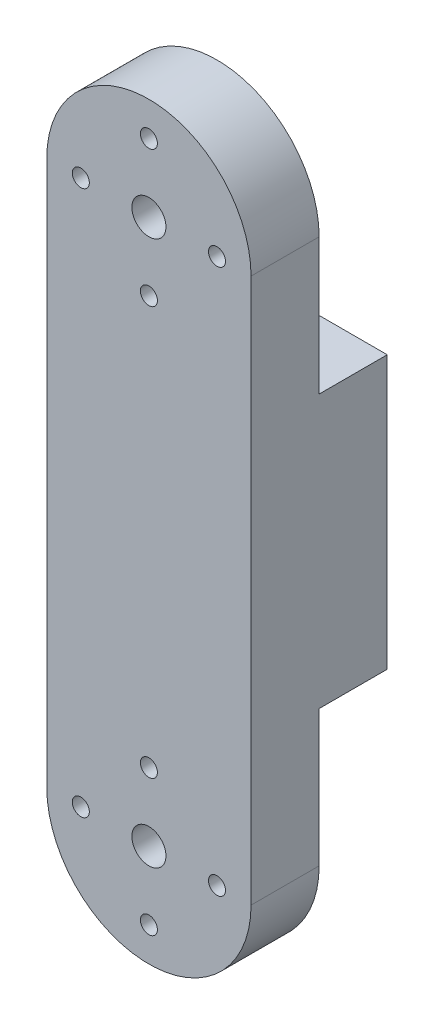
SolidWorks part; units mm, degrees
ref_plane "Front Plane" through (0, 0, 0) normal (0, 0, 1) x (1, 0, 0)
ref_plane "Top Plane" through (0, 0, 0) normal (0, 1, 0) x (1, 0, 0)
ref_plane "Right Plane" through (0, 0, 0) normal (1, 0, 0) x (0, 0, -1)
sketch "Sketch1" plane through (0, 0, 0) normal (0, 0, 1) x (1, 0, 0)
  line L0 (-19.05, 50.8) -> (-19.05, -50.8)
  line L1 (19.05, 50.8) -> (19.05, -50.8)
  line L2 (0, 50.8) -> (0, -50.8) construction
  line L3 (0, 38.1) -> (0, 63.5) construction
  line L4 (-12.7, 50.8) -> (12.7, 50.8) construction
  line L5 (0, -38.1) -> (0, -63.5) construction
  line L6 (-12.7, -50.8) -> (12.7, -50.8) construction
  arc A0 (-19.05, 50.8) -> (19.05, 50.8) centre (0, 50.8) cw
  arc A1 (-19.05, -50.8) -> (19.05, -50.8) centre (0, -50.8) ccw
  circle A2 centre (0, 50.8) radius 3.175
  circle A3 centre (0, -50.8) radius 3.175
  circle A4 centre (0, 63.5) radius 1.5875
  circle A5 centre (-12.7, 50.8) radius 1.5875
  circle A6 centre (0, 38.1) radius 1.5875
  circle A7 centre (12.7, 50.8) radius 1.5875
  circle A8 centre (-12.7, -50.8) radius 1.5875
  circle A9 centre (0, -38.1) radius 1.5875
  circle A10 centre (12.7, -50.8) radius 1.5875
  circle A11 centre (0, -63.5) radius 1.5875
  point P6 (0, 0)
  point P19 (0, 50.8)
  point P21 (0, 50.8)
  point P24 (0, -50.8)
  point P25 (0, -50.8)
  dimension "D3" = 6.35
  dimension "D4" = 3.175
  dimension "D1" = 101.6
  dimension "D2" = 38.1
  dimension "D5" = 12.7
extrude "Boss-Extrude1" add sketch "Sketch1" along normal blind 25.4
sketch "Sketch2" plane through (19.05, 0, 0) normal (1, 0, 0) x (0, 0, -1)
  line L0 (-12.7, 69.85) -> (-12.7, -69.85) construction
  line L1 (0, 69.85) -> (-12.7, 69.85)
  line L2 (0, 69.85) -> (0, 25.4)
  line L3 (0, 25.4) -> (-12.7, 25.4)
  line L4 (-12.7, 69.85) -> (-12.7, 25.4)
  line L5 (0, 69.85) -> (-25.4, 69.85) construction
  line L6 (-25.4, -69.85) -> (0, -69.85) construction
  line L12 (-12.7, -25.4) -> (0, -25.4)
  line L13 (-12.7, -25.4) -> (-12.7, -69.85)
  line L14 (-12.7, -69.85) -> (0, -69.85)
  line L15 (0, -25.4) -> (0, -69.85)
  dimension "D1" = 44.45
extrude "Cut-Extrude1" cut sketch "Sketch2" against normal up to next
